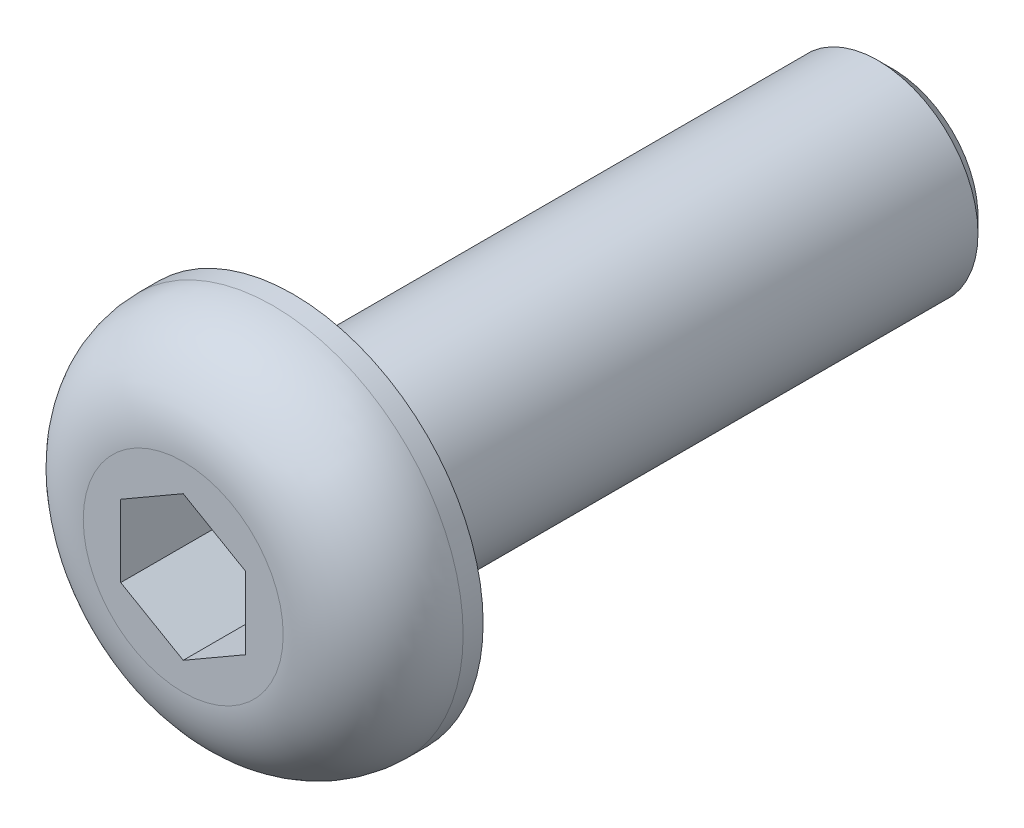
SolidWorks part; units mm, degrees
ref_plane "Front Plane" through (0, 0, 0) normal (0, 0, 1) x (1, 0, 0)
ref_plane "Top Plane" through (0, 0, 0) normal (0, 1, 0) x (1, 0, 0)
ref_plane "Right Plane" through (0, 0, 0) normal (1, 0, 0) x (0, 0, -1)
sketch "Sketch1" plane through (0, 0, 0) normal (0, 0, 1) x (1, 0, 0)
  circle A0 centre (0, 0) radius 3.8
  dimension "D1" = 7.6
extrude "Boss-Extrude1" add sketch "Sketch1" along normal blind 2.2
sketch "Sketch2" plane through (0, 0, 0) normal (0, 0, -1) x (-1, 0, 0)
  circle A0 centre (0, 0) radius 2
  dimension "D1" = 4
extrude "Boss-Extrude2" add sketch "Sketch2" along normal blind 12
chamfer "Chamfer1" distance 0.3 angle 45 1 edges at (-2, 0, -12)
sketch "Sketch3" plane through (0, 0, 2.2) normal (0, 0, 1) x (1, 0, 0)
  line L1 (0, 1.4434) -> (-1.25, 0.7217)
  line L2 (-1.25, 0.7217) -> (-1.25, -0.7217)
  line L3 (-1.25, -0.7217) -> (0, -1.4434)
  line L4 (0, -1.4434) -> (1.25, -0.7217)
  line L5 (1.25, -0.7217) -> (1.25, 0.7217)
  line L6 (1.25, 0.7217) -> (0, 1.4434)
  circle A0 centre (0, 0) radius 1.25 construction
  dimension "D1" = 2.5
extrude "Cut-Extrude1" cut sketch "Sketch3" against normal blind 2
fillet "Fillet1" radius 1.8 1 edges at (3.8, 0, 2.2)
